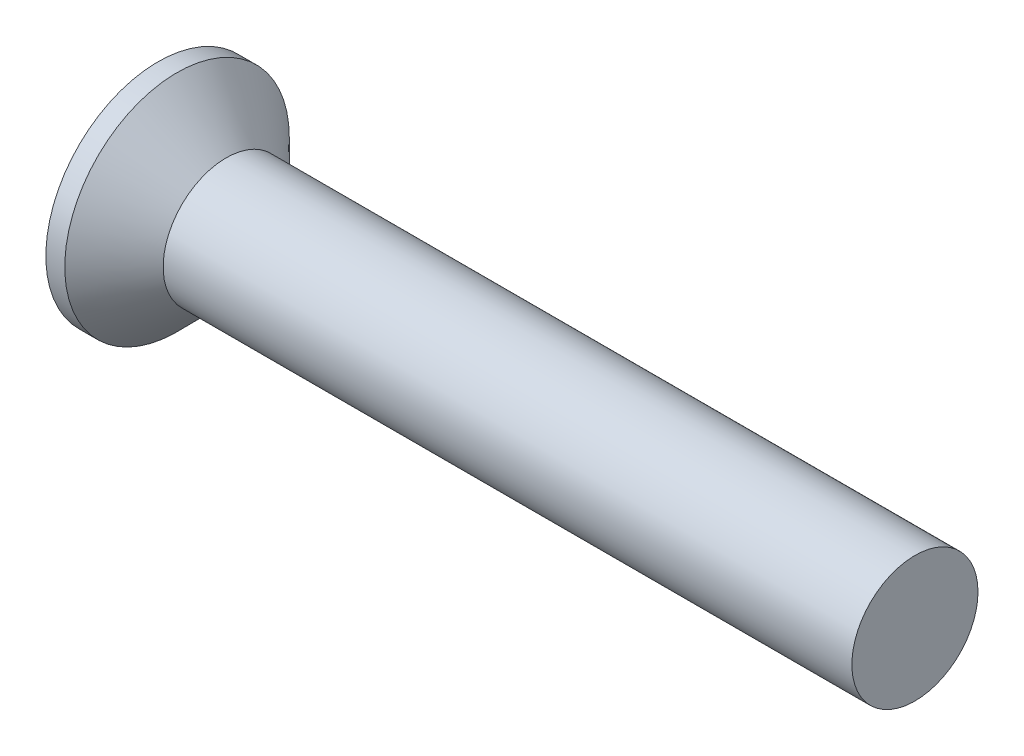
SolidWorks part; units mm, degrees
ref_plane "Front" through (0, 0, 0) normal (0, 0, 1) x (1, 0, 0)
ref_plane "Top" through (0, 0, 0) normal (0, 1, 0) x (1, 0, 0)
ref_plane "Right" through (0, 0, 0) normal (1, 0, 0) x (0, 0, -1)
sketch "Sketch1" plane through (0, 0, 0) normal (0, 0, 1) x (1, 0, 0)
  line L0 (30, 2.5) -> (4.3, 2.5)
  line L1 (4.3, 2.5) -> (2.7, 2.5)
  line L2 (2.7, 2.5) -> (0.75, 4.45)
  line L3 (0.75, 4.45) -> (0, 4.45)
  line L4 (30, 2.5) -> (30, 0)
  line L5 (4.5158, 0) -> (-89.8219, 0) construction
  line L6 (30, 0) -> (0, 0)
  line L7 (0, 4.45) -> (0, 0)
  dimension "d" = 5
  dimension "D1" = 45
  dimension "dk" = 8.9
  dimension "k" = 2.7
  dimension "l" = 30
  dimension "a" = 1.6
revolve "Base" add sketch "Sketch1" angle 360 about L5
cosmetic thread "ThreadCosmetic1" [suppressed] parameters "bb"=47.3, "THD_MINOR"=4.134
sketch "Sketch6" plane through (0, 0, 0) normal (1, 0, 0) x (0, 0, -1)
  line L0 (-1.9271, 0) -> (2.0512, 0) construction
  line L1 (0, 1.8651) -> (0, -2.0207) construction
  line L2 (0.52, 0.52) -> (0.52, 2.6)
  line L3 (0.52, 2.6) -> (-0.52, 2.6)
  line L4 (-0.52, 0.52) -> (-0.52, 2.6)
  line L5 (0.52, 0.52) -> (2.6, 0.52)
  line L6 (2.6, 0.52) -> (2.6, -0.52)
  line L7 (-2.6, 0.52) -> (-2.6, -0.52)
  line L8 (-0.52, 0.52) -> (-2.6, 0.52)
  line L9 (-0.52, -0.52) -> (-2.6, -0.52)
  line L10 (0.52, -0.52) -> (2.6, -0.52)
  line L11 (-0.52, -0.52) -> (-0.52, -2.6)
  line L12 (0.52, -2.6) -> (-0.52, -2.6)
  line L13 (0.52, -0.52) -> (0.52, -2.6)
  point P16 (-2.6, 0)
  point P17 (2.6, 0)
extrude "CrossRecess" cut sketch "Sketch6" along normal blind 1.35
draft "Draft9" type of draft neutral plane draft angle 30 faces to draft 4 face at (0.675, -2.6, 0) face at (0.675, 0, 2.6) face at (0.675, 0, -2.6) face at (0.675, 2.6, 0) neutral plane through (0, 4.45, 0) neutral plane normal (-1, 0, 0) parameters "D1"=30
fillet "Fillet5" radius 0.3 4 edges at (0.675, -0.52, -0.52) (0.675, -0.52, 0.52) (0.675, 0.52, -0.52) (0.675, 0.52, 0.52)
sketch "Sketch7" plane through (0, 0, 0) normal (1, 0, 0) x (0, 0, -1)
  line L0 (-2.0126, 0) -> (1.9757, 0) construction
  line L1 (0, 1.9314) -> (0, -2.0126) construction
  line L2 (0, 0) -> (1.5555, 1.5555) construction
  line L3 (0, 0.777) -> (1.8385, 1.8385)
  line L4 (-1.5402, 1.5402) -> (0, 0) construction
  line L5 (0.777, 0) -> (1.8385, 1.8385)
  line L6 (0, -0.777) -> (1.8385, -1.8385)
  line L7 (0.777, 0) -> (1.8385, -1.8385)
  line L8 (-0.777, 0) -> (-1.8385, -1.8385)
  line L9 (0, -0.777) -> (-1.8385, -1.8385)
  line L10 (-0.777, 0) -> (-1.8385, 1.8385)
  line L11 (0, 0.777) -> (-1.8385, 1.8385)
  dimension "D3" = 15
  dimension "m" = 5.2
extrude "Cut-Extrude3" [suppressed] cut sketch "Sketch7" along normal blind 10 draft 20
sketch "Sketch10" plane through (0, 0, 0) normal (0, 0, 1) x (1, 0, 0)
  line L0 (62.2289, 0) -> (-1.9277, 0) construction
  line L1 (2.7, 2.5) -> (3.5, 2.5)
  line L4 (3.5, 2.5) -> (3.5, 0)
  line L7 (3.5, 0) -> (2.7, 0)
  line L9 (2.7, 2.5) -> (0.75, 4.45) construction
  line L10 (2.7, 2.5) -> (2.7, 0)
  dimension "p" = 0.8
revolve "Revolve2" add sketch "Sketch10" angle 360 about L0
sketch "Sketch8" plane through (0, 0, 0) normal (0, 0, 1) x (1, 0, 0)
  line L0 (-8, 2.5) -> (-10, 2.067)
  line L1 (-10, 2.067) -> (5, 2.067)
  line L3 (30, -2.5) -> (30, 2.5) construction
  line L6 (5, 2.067) -> (5, 7.067)
  line L7 (5, 7.067) -> (-8, 7.067)
  line L8 (-8, 7.067) -> (-8, 2.5)
  line L9 (62.4753, 0) -> (52.9594, 0) construction
  dimension "D1" = 5
  dimension "x" = 2
  dimension "d" = 5
  dimension "THD_MINOR" = 4.134
  dimension "b" = 38
sketch "Sketch11" plane through (0, 0, 0) normal (0, 0, 1) x (1, 0, 0)
  line L0 (30, 2.125) -> (30.2165, 2.5)
  line L1 (30.2165, 2.5) -> (30.2165, 2.933)
  line L2 (30.2165, 2.933) -> (29.7835, 2.933)
  line L3 (29.7835, 2.933) -> (29.7835, 2.5)
  line L4 (29.7835, 2.5) -> (30, 2.125)
  line L5 (30, -2.5) -> (30, 2.5) construction
  line L6 (0, 0) -> (66.0064, 0) construction
  dimension "D1" = 5
  dimension "D2" = 0.433
revolve "Cut-Revolve10" [suppressed] cut sketch "Sketch11" angle 360 about L6
pattern_linear "LPattern10" [suppressed] count 91 spacing 0.5196 along (1, 0, 0)
equation "\"D1@Sketch6\" = \"m@Sketch6\" / 5"
equation "\"D1@CrossRecess\" = \"k@Sketch1\" / 2"
equation "\"D1@Sketch11\" = \"d@Sketch1\""
equation "\"D2@Sketch11\" =  ( \"d@Sketch1\" - \"THD_MINOR@ThreadCosmetic1\" )  / 2"
equation "\"D3@LPattern10\" = \"D2@Sketch11\" * 1.2"
equation "\"D1@LPattern10\" = \"bb@ThreadCosmetic1\" / \"D3@LPattern10\" "
